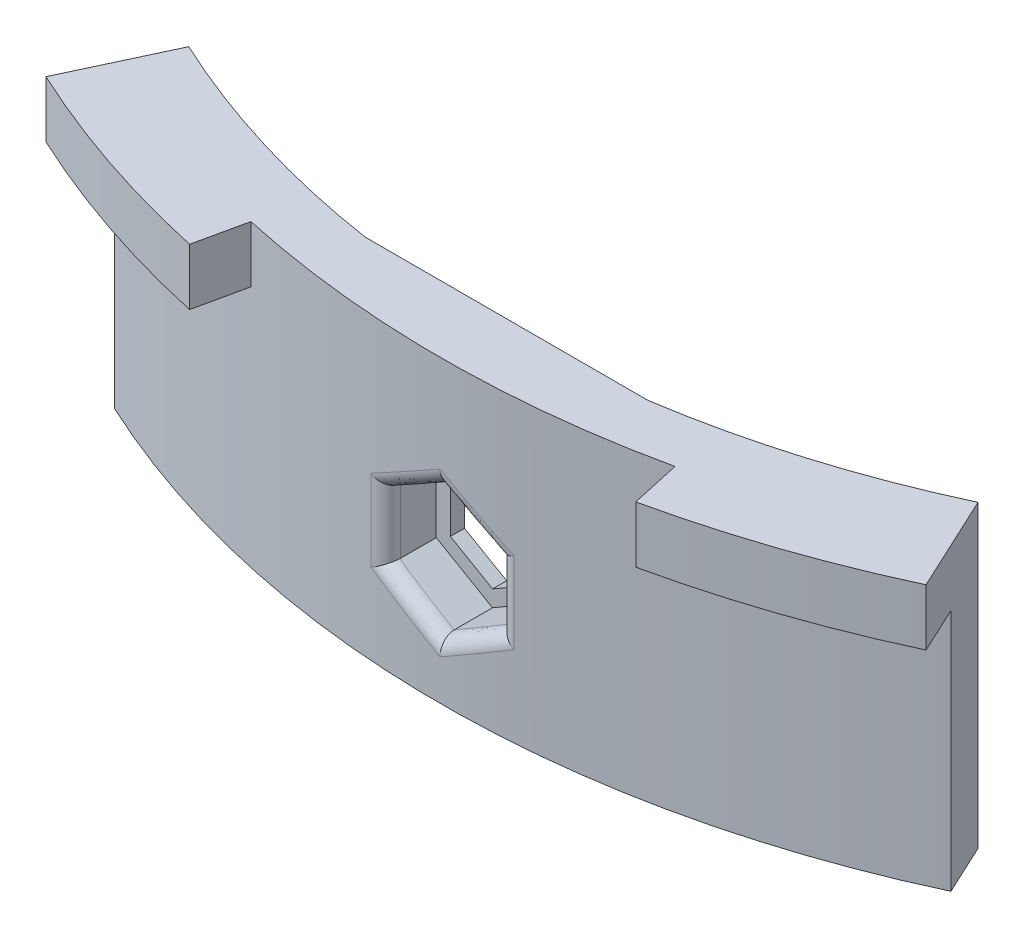
SolidWorks part; units mm, degrees
ref_plane "Front Plane" through (0, 0, 0) normal (0, 0, 1) x (1, 0, 0)
ref_plane "Top Plane" through (0, 0, 0) normal (0, 1, 0) x (1, 0, 0)
ref_plane "Right Plane" through (0, 0, 0) normal (1, 0, 0) x (0, 0, -1)
sketch "Sketch1" plane through (0, 0, 0) normal (0, 0, 1) x (1, 0, 0)
  line L1 (0, 5.842) -> (-5.0593, 2.921)
  line L2 (-5.0593, 2.921) -> (-5.0593, -2.921)
  line L3 (-5.0593, -2.921) -> (0, -5.842)
  line L4 (0, -5.842) -> (5.0593, -2.921)
  line L5 (5.0593, -2.921) -> (5.0593, 2.921)
  line L6 (5.0593, 2.921) -> (0, 5.842)
  line L7 (-12.7, -10.922) -> (12.7, -10.922)
  line L8 (-12.7, -10.922) -> (-12.7, 10.922)
  line L9 (-12.7, 10.922) -> (12.7, 10.922)
  line L10 (12.7, -10.922) -> (12.7, 10.922)
  line L11 (-12.7, -10.922) -> (12.7, 10.922) construction
  line L12 (-12.7, 10.922) -> (12.7, -10.922) construction
  circle A0 centre (0, 0) radius 5.0593 construction
  dimension "D2" = 11.684
  dimension "D1" = 25.4
  dimension "D3" = 5.08
extrude "Bolt Size, Width, &Height" add sketch "Sketch1" along normal blind 7.62
sketch "Sketch2" plane through (0, 10.922, 0) normal (0, 1, 0) x (1, 0, 0)
  line L0 (-12.7, -7.62) -> (-12.7, 0) construction
  line L1 (12.7, -7.62) -> (12.7, 0) construction
  line L6 (12.7, 0) -> (-12.7, 0)
  line L7 (-12.7, 0) -> (-12.7, -7.62)
  line L8 (-12.7, -7.62) -> (12.7, -7.62)
  line L9 (12.7, -7.62) -> (12.7, 0)
  line L10 (12.7, 0) -> (-12.7, 0)
  line L11 (-12.7, 0) -> (-12.7, -7.62)
  line L12 (-12.7, -7.62) -> (12.7, -7.62)
  line L13 (12.7, -7.62) -> (12.7, 0)
  arc A0 (-12.7, -3.81) -> (12.7, -3.81) centre (0, 84.1782) ccw
  line M7 (-12.7, -7.62) -> (12.7, -7.62)
  line M8 (12.7, -7.62) -> (12.7, 0)
  dimension "D1" = 88.9
  dimension "D2" = 0
extrude "Front Curve" cut sketch "Sketch2" against normal through all contours A0 L11 M7 M8
sketch "Sketch3" plane through (0, 0, 0) normal (0, 0, -1) x (-1, 0, 0)
  line L0 (-12.7, -10.922) -> (-12.7, 10.922) construction
  line L1 (-12.7, -10.922) -> (-12.7, 10.922)
  line L2 (-12.7, 10.922) -> (12.7, 10.922) construction
  line L3 (-12.7, 10.922) -> (12.7, 10.922)
  line L4 (12.7, 10.922) -> (12.7, -10.922) construction
  line L5 (12.7, 10.922) -> (12.7, -10.922)
  line L6 (12.7, -10.922) -> (-12.7, -10.922) construction
  line L7 (12.7, -10.922) -> (-12.7, -10.922)
  line L35 (-3.7893, 2.1878) -> (-3.7893, -2.1878)
  line L36 (-3.7893, -2.1878) -> (0, -4.3755)
  line L37 (0, -4.3755) -> (3.7893, -2.1878)
  line L38 (3.7893, -2.1878) -> (3.7893, 2.1878)
  line L39 (3.7893, 2.1878) -> (0, 4.3755)
  line L40 (0, 4.3755) -> (-3.7893, 2.1878)
  line L41 (-3.7893, 2.1878) -> (-3.7893, -2.1878)
  line L42 (-3.7893, -2.1878) -> (0, -4.3755)
  line L43 (0, -4.3755) -> (3.7893, -2.1878)
  line L44 (3.7893, -2.1878) -> (3.7893, 2.1878)
  line L45 (3.7893, 2.1878) -> (0, 4.3755)
  line L46 (0, 4.3755) -> (-3.7893, 2.1878)
  dimension "D1" = 1.27
extrude "Rear Cap" add sketch "Sketch3" along normal blind 1.27
sketch "Sketch6" plane through (0, -10.922, 0) normal (0, -1, 0) x (1, 0, 0)
  line L0 (-37.5708, -3.6074) -> (-35.4472, -8.1614)
  line L1 (37.5708, -3.6074) -> (35.4472, -8.1614)
  line L2 (0, 4.7218) -> (0, -0.3029) construction
  line L3 (-12.7, 3.81) -> (-12.7, -1.27)
  line L4 (-12.7, -1.27) -> (12.7, -1.27)
  line L5 (12.7, -1.27) -> (12.7, 3.81)
  line L6 (-12.7, 3.81) -> (-12.7, -1.27)
  line L7 (-12.7, -1.27) -> (12.7, -1.27)
  line L8 (12.7, -1.27) -> (12.7, 3.81)
  circle A0 centre (0, -84.1782) radius 88.9
  circle A1 centre (0, -84.1782) radius 83.8752
  arc A2 (12.7, 3.81) -> (-12.7, 3.81) centre (0, -84.1782) ccw
  arc A3 (12.7, 3.81) -> (-12.7, 3.81) centre (0, -84.1782) ccw
  line M8 (-12.7, 3.81) -> (-12.7, -1.27)
  line M10 (12.7, -1.27) -> (12.7, 3.81)
  dimension "D2" = 25
  dimension "D3" = 25
  dimension "D1" = 0
extrude "Wings" add sketch "Sketch6" against normal up to surface (21.844 mm away) contours A1 A0 L0 M8 | A1 L1 A0 M10 up to face at (0, 10.922, 1.498)
sketch "Sketch7" plane through (0, 10.922, 0) normal (0, 1, 0) x (1, 0, 0)
  line L1 (-12.7, 1.27) -> (12.7, 1.27) construction
  line L2 (-12.7, 1.27) -> (12.7, 1.27)
  line L3 (-35.4472, 8.1614) -> (-40.5998, -2.8883)
  line L4 (35.4472, 8.1614) -> (40.5998, -2.8883)
  line L5 (-19.05, -2.6568) -> (-20.5858, -9.6575)
  line L6 (19.05, -2.6568) -> (20.5858, -9.6575)
  circle A0 centre (0, 84.1782) radius 96.0672
  arc A1 (-37.5708, 3.6074) -> (37.5708, 3.6074) centre (0, 84.1782) ccw construction
  arc A2 (12.7, 1.27) -> (35.4472, 8.1614) centre (0, 84.1782) ccw construction
  arc A3 (-35.4472, 8.1614) -> (-12.7, 1.27) centre (0, 84.1782) ccw construction
  arc A4 (12.7, 1.27) -> (35.4472, 8.1614) centre (0, 84.1782) ccw
  arc A5 (-35.4472, 8.1614) -> (-12.7, 1.27) centre (0, 84.1782) ccw
  arc A6 (-37.5708, 3.6074) -> (37.5708, 3.6074) centre (0, 84.1782) ccw
  dimension "D1" = 12.192
  dimension "D2" = 38.1
  dimension "D3" = 19.05
extrude "Hook Depth" add sketch "Sketch7" along normal blind 5.08
sketch "Sketch8" plane through (0, 10.922, 0) normal (0, -1, 0) x (1, 0, 0)
  line L0 (0, 4.7218) -> (0, -1.27) construction
  line L1 (12.7, -1.27) -> (-12.7, -1.27) construction
  line L2 (-40.5998, 2.8883) -> (-37.5708, -3.6074)
  line L3 (-19.05, 2.6568) -> (-20.5858, 9.6575)
  line L4 (-40.5998, 2.8883) -> (-37.5708, -3.6074)
  line L5 (-19.05, 2.6568) -> (-20.5858, 9.6575)
  line L6 (40.5998, 2.8883) -> (37.5708, -3.6074)
  line L7 (19.05, 2.6568) -> (20.5858, 9.6575)
  arc A0 (-39.5263, 0.5863) -> (-20.0416, 7.1765) centre (0, -84.1782) cw
  arc A1 (19.05, 2.6568) -> (37.5708, -3.6074) centre (0, -84.1782) cw
  arc A2 (-19.05, 2.6568) -> (-37.5708, -3.6074) centre (0, -84.1782) ccw
  arc A3 (-20.5858, 9.6575) -> (-40.5998, 2.8883) centre (0, -84.1782) ccw
  arc A4 (-19.05, 2.6568) -> (-37.5708, -3.6074) centre (0, -84.1782) ccw
  arc A5 (-20.5858, 9.6575) -> (-40.5998, 2.8883) centre (0, -84.1782) ccw
  arc A6 (20.5858, 9.6575) -> (40.5998, 2.8883) centre (0, -84.1782) cw
  arc A7 (39.5263, 0.5863) -> (20.0416, 7.1765) centre (0, -84.1782) ccw
  line M6 (-40.5998, 2.8883) -> (-37.5708, -3.6074)
  arc M9 (-20.5858, 9.6575) -> (-40.5998, 2.8883) centre (0, -84.1782) ccw
  dimension "D2" = 2.54
  dimension "D3" = 2.54
  dimension "D1" = 0
extrude "Hook Height" add sketch "Sketch8" along normal blind 3.81 contours A0 L5 M6 M9 | A7 L6 A6 L7
fillet "Nut Flange Clearance" radius 1.27 6 edges at (-2.5307, -4.3809, 4.6858) (2.5307, -4.3809, 4.6858) (5.0593, 0, 4.5777) (2.5307, 4.3809, 4.6858) (-2.5307, 4.3809, 4.6858) (-5.0593, 0, 4.5777)
chamfer "Decoration" distance 2.54 angle 45 4 edges at (20.3137, 7.112, 8.417) (40.063, 7.112, 1.7373) (-40.063, 7.112, 1.7373) (-20.3137, 7.112, 8.417)
sketch "Sketch9" plane through (0, 16.002, 0) normal (0, 1, 0) x (1, 0, 0)
  line L0 (-35.4472, 8.1614) -> (-40.5998, -2.8883) construction
  line L1 (40.5998, -2.8883) -> (39.5263, -0.5863)
  line L2 (-39.5263, -0.5863) -> (-40.5998, -2.8883)
  arc A0 (20.0416, -7.1765) -> (39.5263, -0.5863) centre (0, 84.1782) ccw construction
  arc A1 (20.0416, -7.1765) -> (39.5263, -0.5863) centre (0, 84.1782) ccw construction
  arc A2 (39.5263, -0.5863) -> (-39.5263, -0.5863) centre (0, 84.1782) cw
  arc A3 (-40.5998, -2.8883) -> (40.5998, -2.8883) centre (0, 84.1782) ccw
  arc A4 (20.5858, -9.6575) -> (40.5998, -2.8883) centre (0, 84.1782) ccw construction
extrude "Cut-Extrude1" cut sketch "Sketch9" against normal through all
equation "\"D3@Sketch6\"=\"D2@Sketch6\""
equation "\"D3@Sketch7\"=\"D2@Sketch7\"/2"
